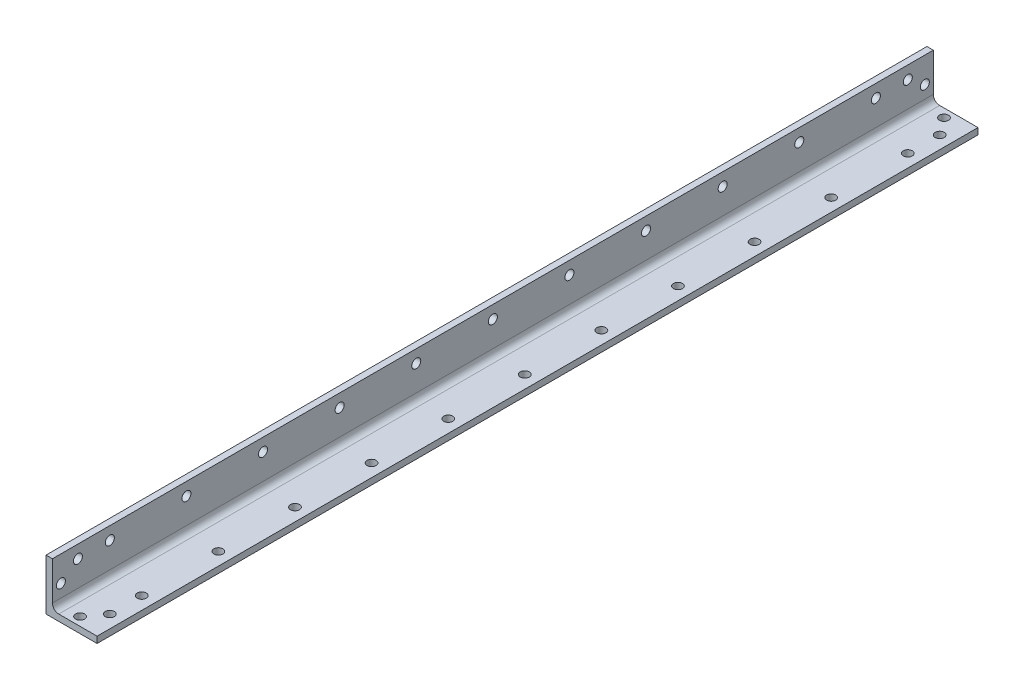
SolidWorks part; units mm, degrees
ref_plane "Front Plane" through (0, 0, 0) normal (0, 0, 1) x (1, 0, 0)
ref_plane "Top Plane" through (0, 0, 0) normal (0, 1, 0) x (1, 0, 0)
ref_plane "Right Plane" through (0, 0, 0) normal (1, 0, 0) x (0, 0, -1)
sketch "Sketch1" plane through (0, 0, 0) normal (0, 0, 1) x (1, 0, 0)
  line L0 (0, 25.4) -> (0, 0)
  line L1 (0, 0) -> (25.4, 0)
  line L2 (25.4, 0) -> (25.4, 3.175)
  line L3 (25.4, 3.175) -> (3.175, 3.175)
  line L4 (3.175, 3.175) -> (3.175, 25.4)
  line L5 (3.175, 25.4) -> (0, 25.4)
  dimension "D1" = 3.175
  dimension "D2" = 25.4
extrude "Boss-Extrude1" add sketch "Sketch1" along normal mid plane 438.15
fillet "Fillet1" radius 3.175 1 edges at (3.175, 3.175, 0)
sketch "Sketch2" plane through (3.175, 0, 0) normal (1, 0, 0) x (0, 0, -1)
  line L0 (-219.075, 25.4) -> (219.075, 25.4) construction
  line L1 (-219.075, 6.35) -> (-219.075, 25.4) construction
  line L2 (0, 3.175) -> (0, 25.4) construction
  line L3 (219.075, 3.175) -> (-219.075, 3.175) construction
  line L4 (-190.5, 19.05) -> (-219.075, 19.05) construction
  line L5 (190.5, 19.05) -> (219.075, 19.05) construction
  line L9 (219.075, 6.35) -> (219.075, 25.4) construction
  circle A0 centre (-214.8417, 12.7) radius 2.25
  circle A1 centre (-206.375, 19.05) radius 2.25
  circle A2 centre (214.8417, 12.7) radius 2.25
  circle A3 centre (206.375, 19.05) radius 2.25
  circle A15 centre (-190.5, 19.05) radius 2.25
  circle A16 centre (-152.4, 19.05) radius 2.25
  circle A17 centre (-114.3, 19.05) radius 2.25
  circle A18 centre (-76.2, 19.05) radius 2.25
  circle A19 centre (-38.1, 19.05) radius 2.25
  circle A20 centre (0, 19.05) radius 2.25
  circle A21 centre (38.1, 19.05) radius 2.25
  circle A22 centre (76.2, 19.05) radius 2.25
  circle A23 centre (114.3, 19.05) radius 2.25
  circle A24 centre (152.4, 19.05) radius 2.25
  circle A25 centre (190.5, 19.05) radius 2.25
  dimension "D1" = 4.5
  dimension "D6" = 6.35
  dimension "D2" = 12.7
  dimension "D3" = 6.35
  dimension "D4" = 12.7
  dimension "D5" = 4.2333
  dimension "D7" = 38.1
ref_plane "Plane1" through (0, 0, 0) normal (0.7071, -0.7071, 0) x (0, 0, -1)
extrude "Cut-Extrude1" cut sketch "Sketch2" against normal through all
mirror "Mirror1" about plane through (0, 0, 0) normal (0.7071, -0.7071, 0) of "Cut-Extrude1"
